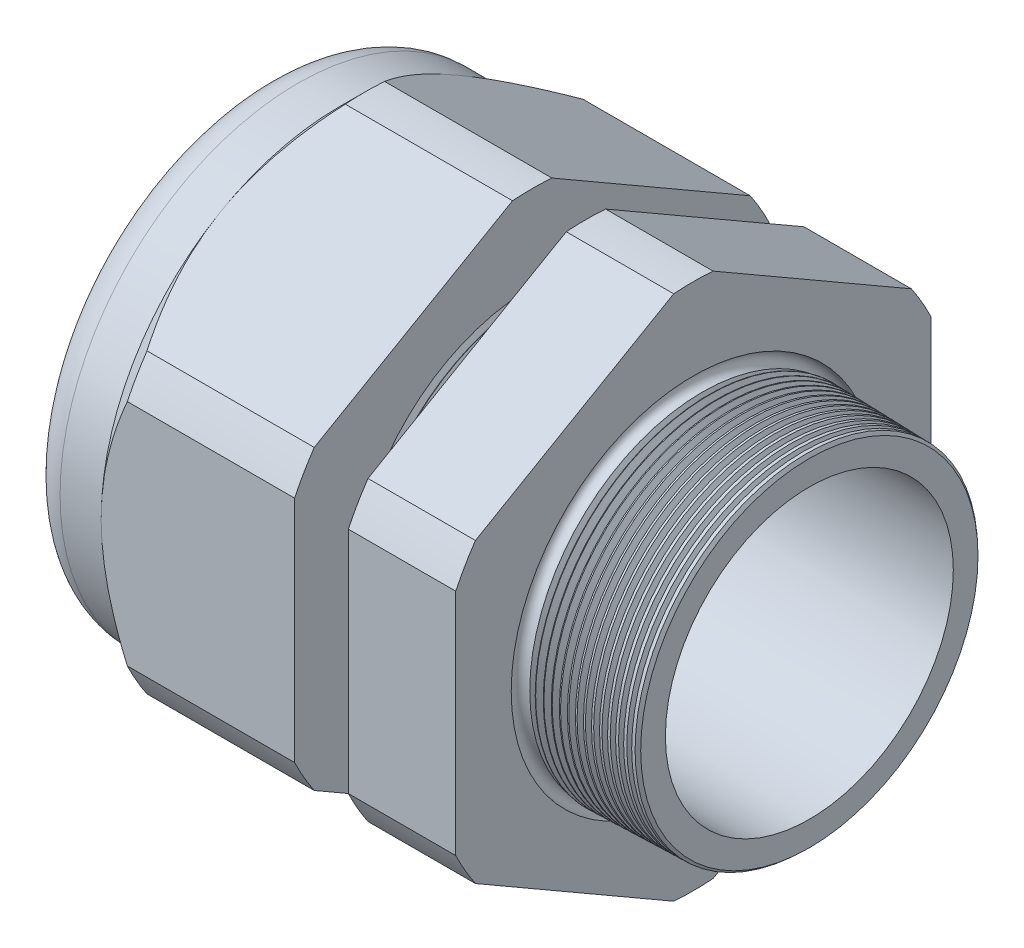
SolidWorks part; units mm, degrees
ref_plane "Front Plane" through (0, 0, 0) normal (0, 0, 1) x (1, 0, 0)
ref_plane "Top Plane" through (0, 0, 0) normal (0, 1, 0) x (1, 0, 0)
ref_plane "Right Plane" through (0, 0, 0) normal (1, 0, 0) x (0, 0, -1)
sketch "Sketch10" plane through (0, 0, 0) normal (0, 0, 1) x (1, 0, 0)
  line L0 (0, 0) -> (-115.3565, 0) construction
  line L1 (-55.88, 16.002) -> (-25.8776, 16.002)
  line L2 (5.08, 16.0803) -> (5.08, 19.1283)
  line L3 (-7.874, 19.4676) -> (5.08, 19.1283)
  line L4 (-7.874, 53.086) -> (-7.874, 19.4676)
  line L5 (-7.874, 53.086) -> (-19.874, 53.086)
  line L6 (-19.874, 53.086) -> (-19.874, 19.7818)
  line L7 (-25.8776, 19.939) -> (-19.874, 19.7818)
  line L8 (-25.8776, 19.939) -> (-25.8776, 53.086)
  line L9 (-25.8776, 53.086) -> (-47.48, 53.086)
  line L10 (-47.48, 53.086) -> (-47.48, 26.543)
  line L11 (-47.48, 26.543) -> (-55.88, 26.543)
  line L12 (-55.88, 26.543) -> (-55.88, 16.002)
  line L13 (-25.8776, 16.002) -> (5.08, 16.0803)
  dimension "D1" = 60.96
  dimension "D2" = 32.004
  dimension "D3" = 1.5
  dimension "D4" = 3.048
  dimension "A" = 39.878
  dimension "D6" = 53.086
  dimension "D8" = 106.172
  dimension "D9" = 8.4
  dimension "D10" = 21.6024
  dimension "D11" = 12
  dimension "D" = 12.954
revolve "Revolve2" add sketch "Sketch10" angle 360 about L0
sketch "Sketch12" plane through (-47.48, 0, 0) normal (-1, 0, 0) x (0, 0, 1)
  line L1 (-2.1972, 29.3807) -> (-24.3458, 16.5931)
  line L2 (-26.543, 12.7876) -> (-26.543, -12.7876)
  line L3 (-24.3458, -16.5931) -> (-2.1972, -29.3807)
  line L4 (2.1972, -29.3807) -> (24.3458, -16.5931)
  line L5 (26.543, -12.7876) -> (26.543, 12.7876)
  line L6 (24.3458, 16.5931) -> (2.1972, 29.3807)
  circle A0 centre (0, 0) radius 26.543 construction
  arc A1 (2.1972, 29.3807) -> (-2.1972, 29.3807) centre (0, 0) ccw
  arc A2 (-24.3458, 16.5931) -> (-26.543, 12.7876) centre (0, 0) ccw
  arc A3 (-26.543, -12.7876) -> (-24.3458, -16.5931) centre (0, 0) ccw
  arc A4 (-2.1972, -29.3807) -> (2.1972, -29.3807) centre (0, 0) ccw
  arc A5 (24.3458, -16.5931) -> (26.543, -12.7876) centre (0, 0) ccw
  arc A6 (26.543, 12.7876) -> (24.3458, 16.5931) centre (0, 0) ccw
  dimension "D2" = 58.9255
  dimension "D1" = 53.086
extrude "Cut-Extrude2" cut sketch "Sketch12" against normal through all flip side to cut
fillet "Fillet4" radius 3.81 1 edges at (-55.88, 0, -26.543)
sketch "Sketch19" plane through (-47.48, 0, 0) normal (-1, 0, 0) x (0, 0, 1)
  line L0 (26.543, 0) -> (26.543, 12.7876) construction
  circle A0 centre (0, 0) radius 26.543
extrude "Cut-Extrude3" cut sketch "Sketch19" against normal blind 3.998 draft 45 flip side to cut
chamfer "Chamfer1" distance 0.254 angle 45 1 edges at (5.08, 0, -19.1283)
sketch "Sketch21" plane through (-55.88, 0, 0) normal (-1, 0, 0) x (0, 0, 1)
  circle A0 centre (0, 0) radius 16.002
  circle A2 centre (0, 0) radius 16.002 construction
extrude "plug" add sketch "Sketch21" against normal blind 12.7 separate body
sketch "Sketch22" plane through (-55.88, 0, 0) normal (-1, 0, 0) x (0, 0, 1)
  circle A0 centre (0, 0) radius 15.748
  circle A1 centre (0, 0) radius 16.002 construction
  dimension "D1" = 0.254
extrude "Cut-Extrude4" cut sketch "Sketch22" against normal blind 0.508
sketch "Sketch27" plane through (-55.372, 0, 0) normal (-1, 0, 0) x (0, 0, 1)
  line L0 (-4.3624, 0) -> (4.3624, 0) construction
  circle A0 centre (-11.7953, 0) radius 3.937
  circle A1 centre (0, 0) radius 15.748 construction
  dimension "D1" = 0.0157
  dimension "holedia" = 7.874
extrude "plugholes" cut sketch "Sketch27" against normal through all
pattern_circular "CirPattern1" count 6 over 360 about axis through (0, 0, 0) along (1, 0, 0) of "plugholes"
sketch "Sketch28" [suppressed] plane through (-29.464, 0, 0) normal (-1, 0, 0) x (0, 0, 1)
  circle A0 centre (0, 0) radius 0.762
  dimension "midholedia" = 7.874
extrude "midhole" [suppressed] cut sketch "Sketch28" against normal through all
sketch "Sketch29" plane through (0, 0, 0) normal (0, 0, 1) x (1, 0, 0)
  line L0 (-25.8776, 19.939) -> (-25.1446, 19.9198)
  line L1 (-19.874, 19.7818) -> (-25.8776, 19.939) construction
  line L2 (-25.1446, 19.9198) -> (-25.5277, 19.2946)
  line L3 (-25.5277, 19.2946) -> (-25.8776, 19.939)
  dimension "D1" = 60
  dimension "D2" = 60
  dimension "D3" = 0.635
revolve "Cut-Revolve1" cut sketch "Sketch29" angle 360 about axis through (0, 0, 0) along (-1, 0, 0)
pattern_linear "LPattern1" count 8 spacing 0.762 along (1, 0, 0) of "Cut-Revolve1"
sketch "Sketch30" plane through (0, 0, 0) normal (0, 0, 1) x (1, 0, 0)
  line L0 (-7.874, 19.4676) -> (-6.9944, 19.4445)
  line L1 (-7.874, 29.3807) -> (-7.874, 16.5931) construction
  line L2 (4.8261, 19.135) -> (-7.874, 19.4676) construction
  line L3 (-6.9944, 19.4445) -> (-7.4542, 18.6943)
  line L4 (-7.4542, 18.6943) -> (-7.874, 19.4676)
  dimension "D1" = 60
  dimension "D2" = 60
  dimension "D3" = 0.762
revolve "Cut-Revolve2" cut sketch "Sketch30" angle 360 about axis through (0, 0, 0) along (-1, 0, 0)
pattern_linear "LPattern2" count 15 spacing 0.889 along (1, 0, 0) of "Cut-Revolve2"
sketch "Sketch31" [suppressed] plane through (-38.354, 0, 0) normal (-1, 0, 0) x (0, 0, 1)
  line L0 (-1.905, 1.905) -> (1.905, 1.905)
  line L1 (-1.905, -1.905) -> (1.905, -1.905)
  circle A0 centre (0, 0) radius 1.905 construction
  arc A1 (-1.905, 1.905) -> (-1.905, -1.905) centre (-1.905, 0) ccw
  arc A2 (1.905, 1.905) -> (1.905, -1.905) centre (1.905, 0) cw
extrude "Cut-Extrude5" [suppressed] cut sketch "Sketch31" against normal through all
sketch "Sketch32" plane through (0, 0, 0) normal (0, 0, 1) x (1, 0, 0)
  line L0 (-7.874, 29.3807) -> (-7.874, 16.5931) construction
  circle A0 centre (-7.747, 19.4676) radius 0.889
  dimension "D2" = 1.778
  dimension "D1" = 0.127
revolve "Cut-Revolve3" cut sketch "Sketch32" angle 360 about axis through (0, 0, 0) along (-1, 0, 0)
